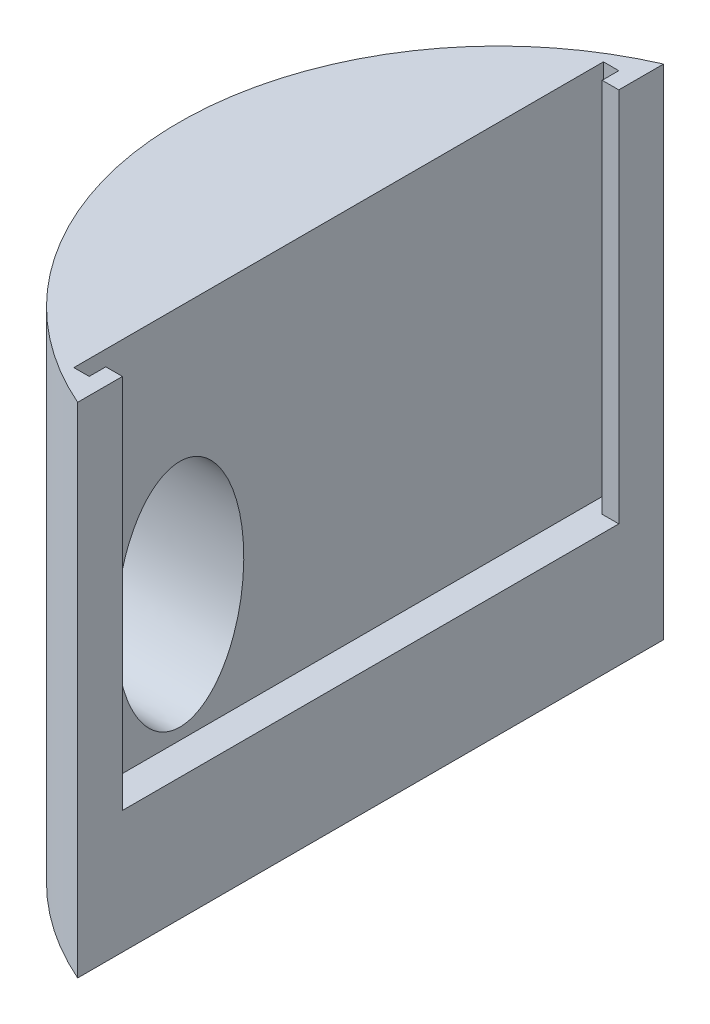
SolidWorks part; units mm, degrees
ref_plane "Front Plane" through (0, 0, 0) normal (0, 0, 1) x (1, 0, 0)
ref_plane "Top Plane" through (0, 0, 0) normal (0, 1, 0) x (1, 0, 0)
ref_plane "Right Plane" through (0, 0, 0) normal (1, 0, 0) x (0, 0, -1)
sketch "Sketch1" plane through (0, 0, 0) normal (0, 1, 0) x (1, 0, 0)
  line L0 (-10, 22.9129) -> (-10, -22.9129)
  line L1 (-10, 22.9129) -> (-10, -22.9129) construction
  arc A0 (-10, 22.9129) -> (-10, -22.9129) centre (0, 0) ccw
  dimension "D1" = 50
extrude "Boss-Extrude1" add sketch "Sketch1" along normal blind 39
sketch "Sketch2" plane through (0, 39, 0) normal (0, 1, 0) x (1, 0, 0)
  line L0 (-12.5, 23.6953) -> (-12.5, -24.4272) construction
  line L1 (-10, -22.9129) -> (-10, 22.9129) construction
  line L2 (6.5307, 19.4129) -> (-33.2969, 19.4129) construction
  line L3 (0, 0) -> (-45.9221, 0) construction
  line L4 (-11.3, -24.4272) -> (-11.3, 23.6953) construction
  line L5 (9.8732, -19.4129) -> (-48.416, -19.4129) construction
  line L6 (-23.5169, -20.7129) -> (7.3254, -20.7129) construction
  line L7 (-33.2969, 20.7129) -> (19.5907, 20.7129) construction
  line L9 (-10, 19.4129) -> (-11.3, 19.4129)
  line L10 (-11.3, 19.4129) -> (-11.3, 20.7129)
  line L11 (-11.3, 20.7129) -> (-12.5, 20.7129)
  line L12 (-12.5, -20.7129) -> (-12.5, 20.7129)
  line L13 (-12.5, -20.7129) -> (-11.3, -20.7129)
  line L14 (-11.3, -20.7129) -> (-11.3, -19.4129)
  line L15 (-11.3, -19.4129) -> (-10, -19.4129)
  line L16 (-10, -19.4129) -> (-10, 19.4129)
  dimension "D1" = 1.2
  dimension "D2" = 1.3
  dimension "D3" = 3.5
  dimension "D4" = 3.5
  dimension "D5" = 1.3
  dimension "D6" = 1.3
extrude "Cut-Extrude1" cut sketch "Sketch2" against normal blind 29.4
sketch "Sketch3" plane through (-12.5, 0, 0) normal (1, 0, 0) x (0, 0, -1)
  line L0 (0, 0) -> (0, 49.6262) construction
  line L1 (-31.518, 19.5) -> (34.9302, 19.5) construction
  line L2 (-22.9129, 0) -> (22.9129, 0) construction
  ellipse E0 centre (-12.4202, 19.5) end of major axis (-12.4202, 28.5) minor radius 5
  dimension "D1" = 19.5
extrude "Cut-Extrude2" cut sketch "Sketch3" against normal through all both and the other way through all
